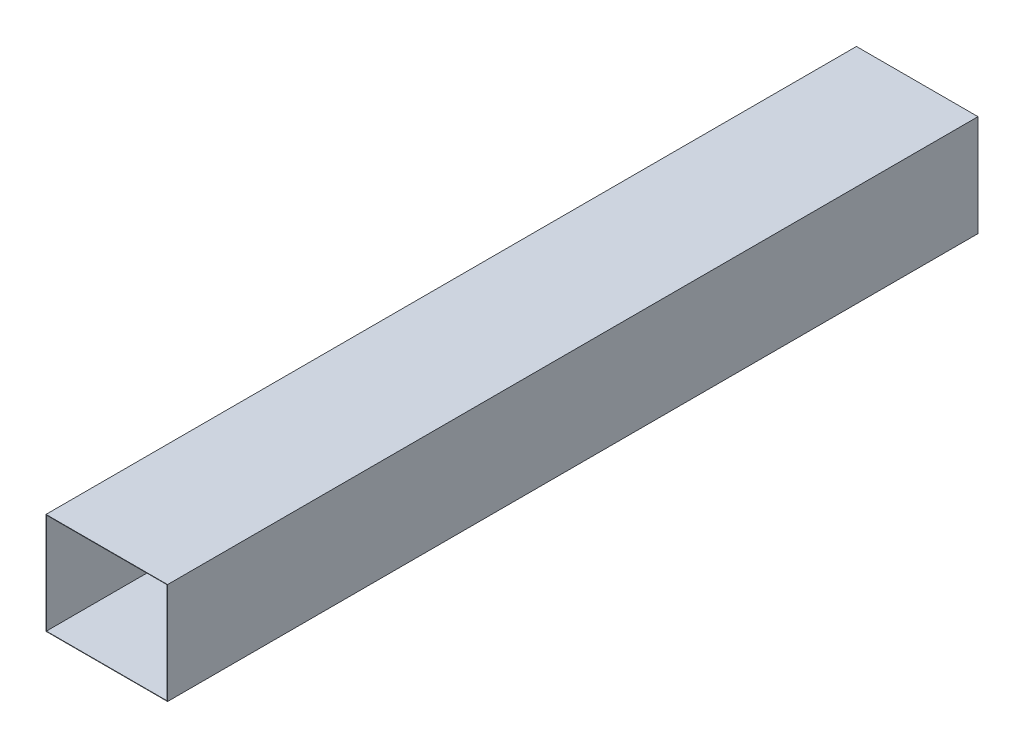
SolidWorks part; units mm, degrees
ref_plane "Front Plane" through (0, 0, 0) normal (0, 0, 1) x (1, 0, 0)
ref_plane "Top Plane" through (0, 0, 0) normal (0, 1, 0) x (1, 0, 0)
ref_plane "Right Plane" through (0, 0, 0) normal (1, 0, 0) x (0, 0, -1)
sketch "Sketch1" plane through (0, 0, 0) normal (0, 0, 1) x (1, 0, 0)
  line L1 (-300, 250) -> (0, 250)
  line L2 (-300, 250) -> (-300, 0)
  line L3 (-300, 0) -> (0, 0)
  line L4 (0, 250) -> (0, 0)
  dimension "D1" = 250
  dimension "D2" = 300
extrude "Extrude-Thin1" add sketch "Sketch1" along normal blind 2000 thin contours L2 L3 L4 L1
